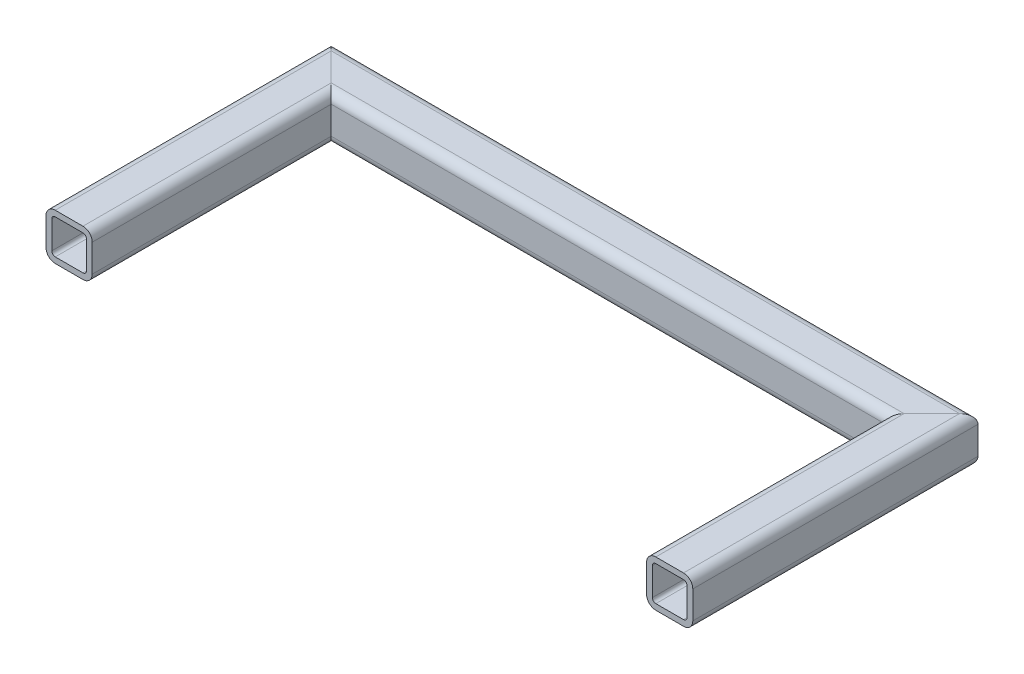
SolidWorks part; units mm, degrees
material "Plain Carbon Steel"
ref_plane "Front" through (0, 0, 0) normal (0, 0, 1) x (1, 0, 0)
ref_plane "Top" through (0, 0, 0) normal (0, 1, 0) x (1, 0, 0)
ref_plane "Right" through (0, 0, 0) normal (1, 0, 0) x (0, 0, -1)
sketch "Sketch1" plane through (0, 0, 0) normal (0, 1, 0) x (1, 0, 0)
  line L0 (-220.3771, 76.5578) -> (109.8229, 76.5578)
  line L1 (109.8229, 76.5578) -> (109.8229, -67.5618)
  line L2 (-220.3771, 76.5578) -> (-220.3771, -67.5618)
  dimension "D1" = 330.2
  dimension "D2" = 144.1196
  dimension "D3" = 220.3771
  dimension "D4" = 76.5578
  dimension "D5" = 144.1196
other "Square tubing 1 X 1 X 0.125(1)"
ref_plane "Plane1" through (-220.3771, 0, -76.5578) normal (1, 0, 0) x (0, 0, -1)
sketch "Sketch12" plane through (-220.3771, 0, -76.5578) normal (1, 0, 0) x (0, 0, -1)
  line L0 (-7.62, -9.525) -> (7.62, -9.525)
  line L1 (-9.525, -7.62) -> (-9.525, 7.62)
  line L2 (7.62, 9.525) -> (-7.62, 9.525)
  line L3 (9.525, 7.62) -> (9.525, -7.62)
  line L4 (-7.62, -12.7) -> (7.62, -12.7)
  line L5 (-12.7, -7.62) -> (-12.7, 7.62)
  line L6 (7.62, 12.7) -> (-7.62, 12.7)
  line L7 (12.7, 7.62) -> (12.7, -7.62)
  line L8 (0, 0) -> (9.525, 0) construction
  line L9 (0, 0) -> (0, 9.525) construction
  arc A0 (12.7, 7.62) -> (7.62, 12.7) centre (7.62, 7.62) ccw
  arc A1 (7.62, -12.7) -> (12.7, -7.62) centre (7.62, -7.62) ccw
  arc A2 (-12.7, -7.62) -> (-7.62, -12.7) centre (-7.62, -7.62) ccw
  arc A3 (-7.62, 12.7) -> (-12.7, 7.62) centre (-7.62, 7.62) ccw
  arc A4 (-7.62, 9.525) -> (-9.525, 7.62) centre (-7.62, 7.62) ccw
  arc A5 (9.525, 7.62) -> (7.62, 9.525) centre (7.62, 7.62) ccw
  arc A6 (7.62, -9.525) -> (9.525, -7.62) centre (7.62, -7.62) ccw
  arc A7 (-9.525, -7.62) -> (-7.62, -9.525) centre (-7.62, -7.62) ccw
  point P3 (0, 12.7)
  point P4 (12.7, 0)
  point P5 (0, -12.7)
  point P6 (-12.7, 0)
  point P7 (-12.7, 12.7)
  point P8 (-12.7, -12.7)
  point P33 (0, 0)
  point P35 (12.7, -12.7)
  point P36 (12.7, 12.7)
  point P37 (0, 0)
  dimension "D1" = 5.08
  dimension "Thickness" = 3.175
  dimension "V_leg" = 25.4
equation "\"Total Cutting Length\"= \"Cutting Length-Outer\" + \"Cutting Length-Inner\""
equation "\"Amount in ft^2\"= \"Bounding Box Area-Blank\" / 144"
